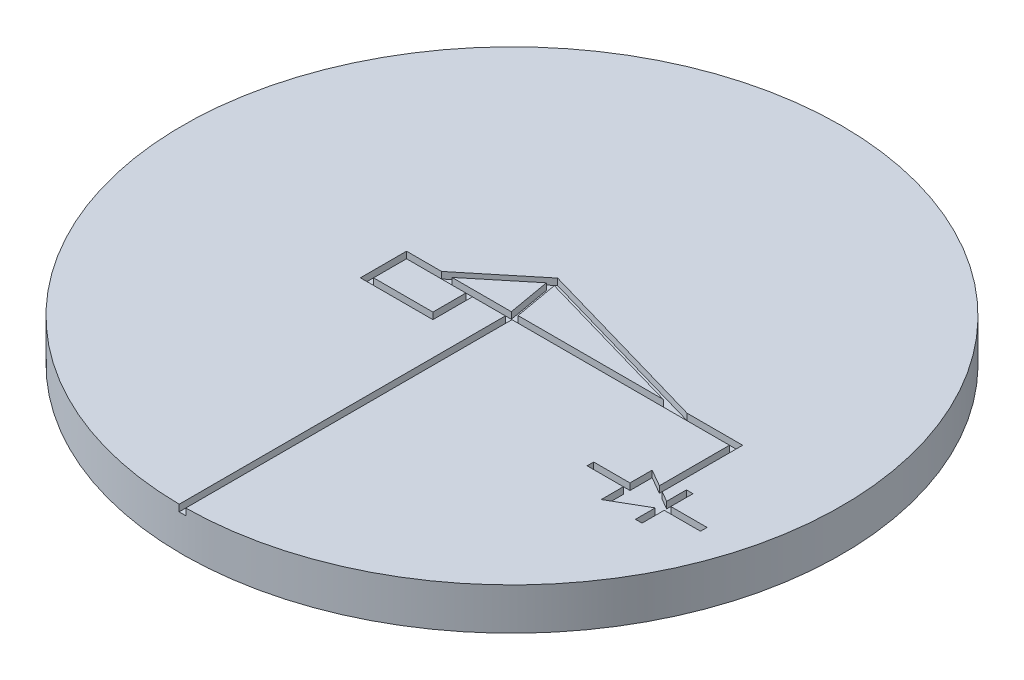
SolidWorks part; units mm, degrees
material "ABS PC"
ref_plane "Front Plane" through (0, 0, 0) normal (0, 0, 1) x (1, 0, 0)
ref_plane "Top Plane" through (0, 0, 0) normal (0, 1, 0) x (1, 0, 0)
ref_plane "Right Plane" through (0, 0, 0) normal (1, 0, 0) x (0, 0, -1)
sketch "Sketch1" plane through (0, 0, 0) normal (0, 1, 0) x (1, 0, 0)
  circle A0 centre (0, 0) radius 25
  dimension "D1" = 50
extrude "Boss-Extrude1" add sketch "Sketch1" along normal blind 3.175
sketch "Sketch2" plane through (0, 3.175, 0) normal (0, 1, 0) x (1, 0, 0)
  line L0 (0, 0) -> (0, -25) construction
  line L1 (-8, 0) -> (17, 0) construction
  line L2 (0, 0) -> (-0.6946, 3.9392) construction
  line L3 (-0.6946, 3.9392) -> (-5.5, 0) construction
  line L4 (-8, 0) -> (-8, -3) construction
  line L5 (-8, -3) -> (-3, -3) construction
  line L6 (-3, -3) -> (-3, 0) construction
  line L7 (-0.6946, 3.9392) -> (13, 0) construction
  line L8 (17, 0) -> (17, -6) construction
  line L9 (18.299, -6.75) -> (15.701, -5.25) construction
  line L10 (15.701, -5.25) -> (15.701, -8.25) construction
  line L11 (15.701, -8.25) -> (18.299, -6.75) construction
  line L12 (18.299, -5.25) -> (18.299, -8.25) construction
  line L13 (18.299, -6.75) -> (21.299, -6.75) construction
  line L14 (15.701, -6.75) -> (12.701, -6.75) construction
  line L15 (17.25, 0.25) -> (17.25, -5.8557)
  line L16 (-8.25, 0.25) -> (-5.5894, 0.25)
  line L17 (-8.25, 0.25) -> (-8.25, -3.25)
  line L18 (-8.25, -3.25) -> (-2.75, -3.25)
  line L19 (-2.75, -3.25) -> (-2.75, -0.25)
  line L20 (-0.8531, 4.1326) -> (-5.5894, 0.25)
  line L21 (-0.8531, 4.1326) -> (-5.6585, 0.1933) construction
  line L22 (-4.8007, 0.25) -> (-0.2979, 0.25)
  line L23 (0.2098, 0.25) -> (-0.3789, 3.5883)
  line L25 (15.451, -4.817) -> (15.451, -6.5)
  line L26 (15.451, -8.683) -> (18.049, -7.183)
  line L27 (18.049, -5.25) -> (18.049, -6.317)
  line L28 (18.549, -7) -> (21.299, -7)
  line L29 (15.451, -6.5) -> (12.701, -6.5)
  line L30 (16.75, -0.25) -> (16.75, -5.567)
  line L31 (-7.75, -0.25) -> (-3.25, -0.25)
  line L32 (-7.75, -0.25) -> (-7.75, -2.75)
  line L33 (-7.75, -2.75) -> (-3.25, -2.75)
  line L34 (-3.25, -2.75) -> (-3.25, -0.25)
  line L35 (-0.8531, 4.1326) -> (-0.7516, 4.2158)
  line L36 (-0.6255, 4.1795) -> (13.0352, 0.25)
  line L37 (-0.25, -0.25) -> (-0.25, -24.9987)
  line L38 (-8.25, 0.25) -> (17.25, 0.25) construction
  line L42 (18.549, -5.25) -> (18.549, -6.5)
  line L43 (18.549, -6.5) -> (21.299, -6.5)
  line L44 (15.451, -7) -> (12.701, -7)
  line L45 (-0.6255, 4.1795) -> (-0.7516, 4.2158)
  line L46 (-0.6255, 4.1795) -> (13.0691, 0.2403) construction
  line L47 (-0.8666, 3.475) -> (-4.8007, 0.25)
  line L48 (-0.3789, 3.5883) -> (11.2265, 0.25)
  line L49 (-0.25, -0.0219) -> (-0.9408, 3.8958) construction
  line L50 (0.25, 0.0219) -> (-0.4484, 3.9826) construction
  line L51 (-3.25, -2.75) -> (-3.25, 0) construction
  line L52 (-2.75, -3.25) -> (-2.75, 0) construction
  line L53 (-0.2979, 0.25) -> (-0.8666, 3.475)
  line L54 (0.25, -0.25) -> (0.25, -24.9987)
  line L55 (0.25, 0.0219) -> (0.25, -25) construction
  line L56 (-0.25, -0.0219) -> (-0.25, -25) construction
  line L57 (13.0352, 0.25) -> (17.25, 0.25)
  line L58 (-2.75, -0.25) -> (-0.25, -0.25)
  line L59 (-7.75, -0.25) -> (16.75, -0.25) construction
  line L60 (0.2098, 0.25) -> (11.2265, 0.25)
  line L61 (16.75, -0.25) -> (16.75, -6) construction
  line L62 (17.25, 0.25) -> (17.25, -6) construction
  line L63 (18.049, -7.183) -> (18.049, -8.25)
  line L64 (18.049, -5.25) -> (18.049, -8.25) construction
  line L65 (18.299, -6.5) -> (21.299, -6.5) construction
  line L66 (18.299, -7) -> (21.299, -7) construction
  line L67 (18.799, -6.75) -> (15.451, -4.817) construction
  line L68 (15.451, -8.683) -> (18.799, -6.75) construction
  line L69 (18.549, -7) -> (18.549, -8.25)
  line L70 (18.549, -5.25) -> (18.549, -8.25) construction
  line L71 (18.049, -6.317) -> (17.25, -5.8557)
  line L72 (15.451, -7) -> (15.451, -8.683)
  line L73 (15.451, -4.817) -> (15.451, -8.683) construction
  line L74 (15.701, -7) -> (12.701, -7) construction
  line L75 (15.701, -6.5) -> (12.701, -6.5) construction
  line L76 (12.701, -7) -> (12.701, -6.5)
  line L77 (18.049, -8.25) -> (18.049, -8.683)
  line L78 (18.049, -8.683) -> (18.549, -8.683)
  line L79 (18.549, -8.683) -> (18.549, -8.25)
  line L80 (18.049, -5.25) -> (18.049, -4.817)
  line L81 (18.049, -4.817) -> (18.549, -4.817)
  line L82 (18.549, -4.817) -> (18.549, -5.25)
  line L83 (21.299, -6.5) -> (21.299, -7)
  line L84 (16.75, -5.567) -> (15.451, -4.817)
  line L85 (0.25, -0.25) -> (16.75, -0.25)
  circle A0 centre (0, 0) radius 25 construction
  arc A1 (-0.25, -24.9987) -> (0.25, -24.9987) centre (0, 0) ccw
  point P13 (-5.5, -3)
  point P25 (17, -6)
  dimension "D1" = 3
  dimension "D2" = 5
  dimension "D3" = 8
  dimension "D4" = 4
  dimension "D5" = 80
  dimension "D6" = 4
  dimension "D7" = 3
  dimension "D8" = 6
  dimension "D9" = 3
  dimension "D10" = 17
  dimension "D11" = 0.25
  dimension "D12" = 0.25
extrude "Cut-Extrude1" cut sketch "Sketch2" against normal blind 0.5
